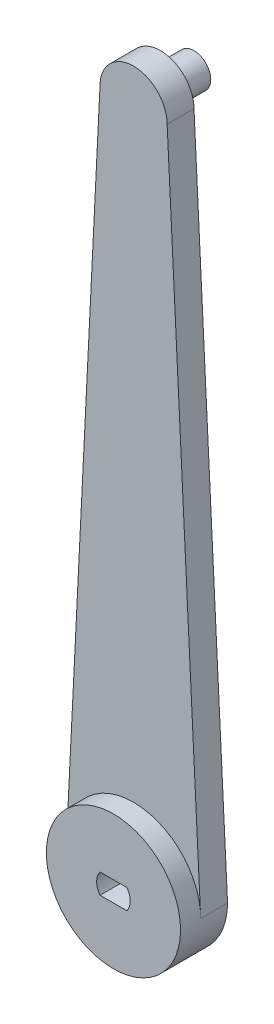
SolidWorks part; units mm, degrees
ref_plane "Front Plane" through (0, 0, 0) normal (0, 0, 1) x (1, 0, 0)
ref_plane "Top Plane" through (0, 0, 0) normal (0, 1, 0) x (1, 0, 0)
ref_plane "Right Plane" through (0, 0, 0) normal (1, 0, 0) x (0, 0, -1)
sketch "Sketch2" plane through (0, 0, 0) normal (0, 0, 1) x (1, 0, 0)
  line L0 (0, 0) -> (0, 1.5) construction
  line L1 (0, 0) -> (0, -1.5) construction
  line L2 (-2, -1.5) -> (2, -1.5)
  line L3 (-2, 1.5) -> (2, 1.5)
  arc A0 (-2, 1.5) -> (-2, -1.5) centre (0, 0) ccw
  arc A1 (2, -1.5) -> (2, 1.5) centre (0, 0) ccw
  point P9 (0, 0)
  point P10 (0, 0)
sketch "Sketch3" plane through (0, 0, 0) normal (0, 0, 1) x (1, 0, 0)
  line L0 (0, 0) -> (0, 100) construction
  line L1 (-10, 0) -> (-5, 100)
  line L2 (5, 100) -> (10, 0)
  arc A0 (-10, 0) -> (10, 0) centre (0, 0) ccw
  arc A1 (5, 100) -> (-5, 100) centre (0, 100) ccw
extrude "Boss-Extrude1" add sketch "Sketch3" along normal blind 4
sketch "Sketch4" plane through (0, 0, 4) normal (0, 0, 1) x (1, 0, 0)
  circle A0 centre (0, 0) radius 10
extrude "Boss-Extrude2" add sketch "Sketch4" along normal blind 3
sketch "Sketch5" plane through (0, 0, 4) normal (0, 0, 1) x (1, 0, 0)
  line L0 (-5, 100) -> (5, 100) construction
  line L1 (0, 100) -> (0, 0) construction
  circle A0 centre (0, 100) radius 2.5
extrude "Cut-Extrude3" cut sketch "Sketch2" along normal blind 11
extrude "Boss-Extrude4" add sketch "Sketch5" against normal blind 9
